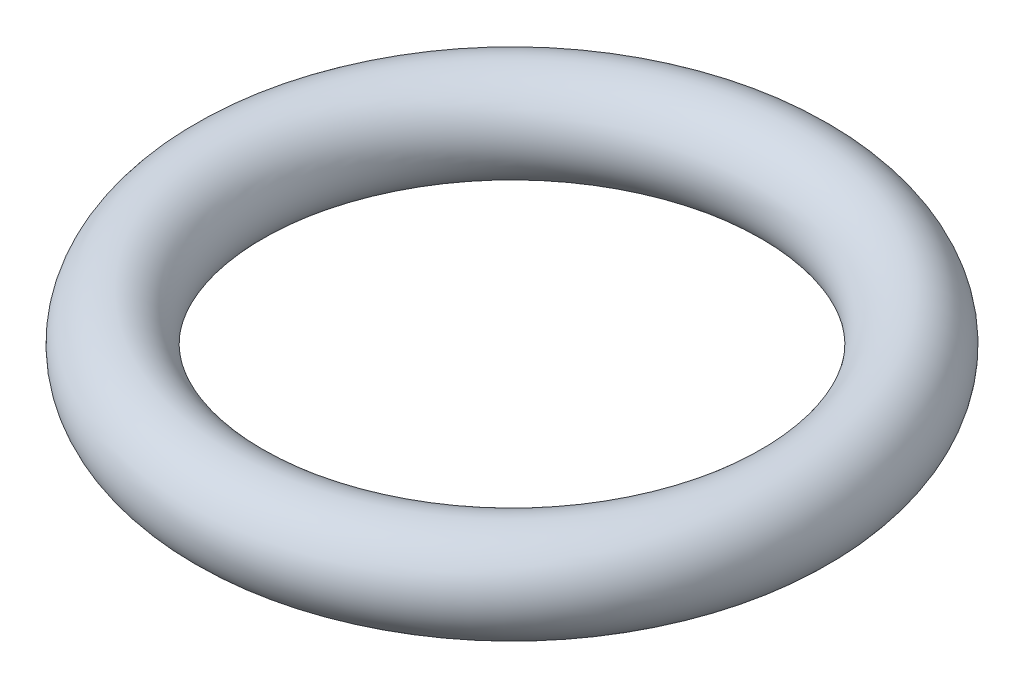
SolidWorks part; units mm, degrees
ref_plane "Front Plane" through (0, 0, 0) normal (0, 0, 1) x (1, 0, 0)
ref_plane "Top Plane" through (0, 0, 0) normal (0, 1, 0) x (1, 0, 0)
ref_plane "Right Plane" through (0, 0, 0) normal (1, 0, 0) x (0, 0, -1)
sketch "Sketch1" plane through (0, 0, 0) normal (0, 1, 0) x (1, 0, 0)
  circle A0 centre (0, 0) radius 152.4
  dimension "D1" = 304.8
sweep "Sweep1" add path "Sketch1" circular profile diameter 50.8 parameters "D3"=50.8
